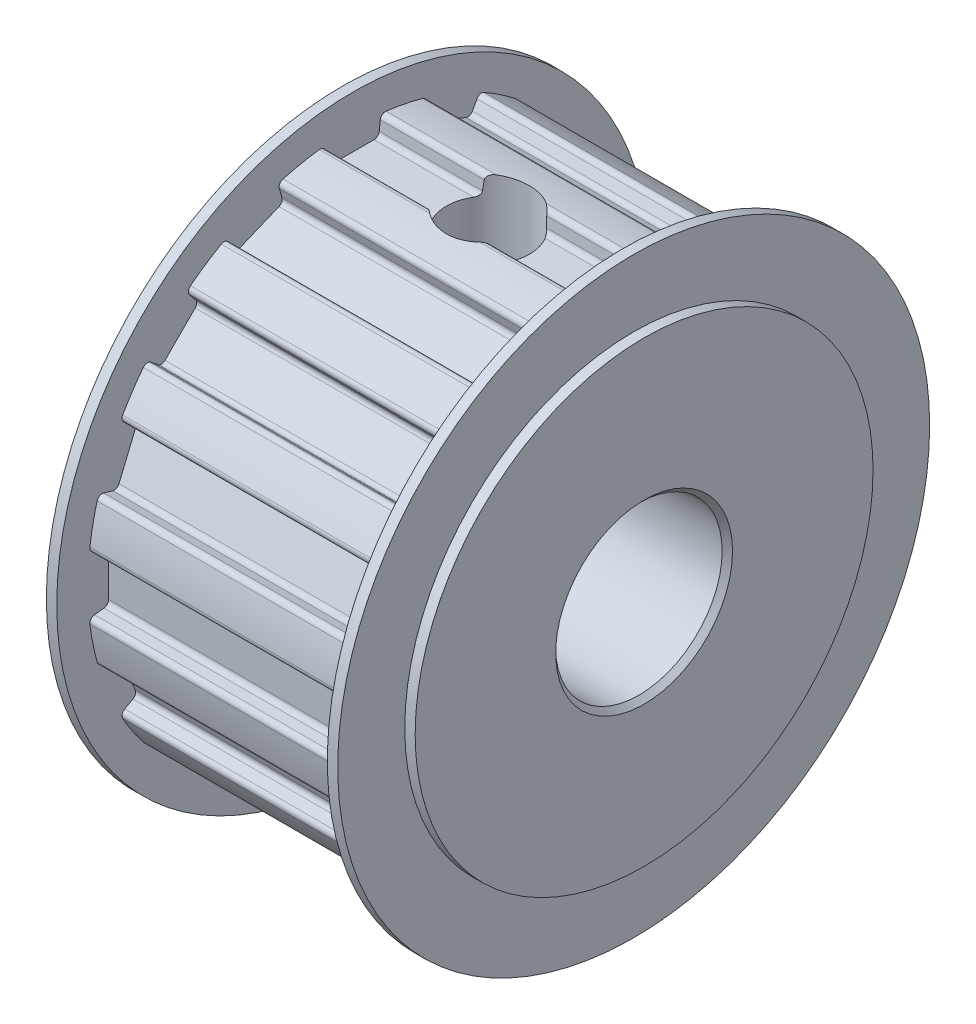
SolidWorks part; units mm, degrees
ref_plane "Plan de face" through (0, 0, 0) normal (0, 0, 1) x (1, 0, 0)
ref_plane "Plan de dessus" through (0, 0, 0) normal (0, 1, 0) x (1, 0, 0)
ref_plane "Plan de droite" through (0, 0, 0) normal (1, 0, 0) x (0, 0, -1)
sketch "Esquisse1" plane through (0, 0, 0) normal (1, 0, 0) x (0, 0, -1)
  circle A0 centre (0, 0) radius 12.73
  dimension "D1" = 25.46
extrude "Extrusion1" add sketch "Esquisse1" along normal blind 13
sketch "Esquisse22" plane through (0, 0, 0) normal (-1, 0, 0) x (0, 0, 1)
  line L0 (0, 0) -> (0, 12.73) construction
  line L1 (-1.25, 11.73) -> (1.25, 11.73)
  line L2 (0, 0) -> (1.25, 11.73) construction
  line L3 (0, 0) -> (-1.25, 11.73) construction
  line L4 (-1.25, 11.73) -> (-2.6986, 25.3234)
  line L5 (1.25, 11.73) -> (2.6979, 25.3172)
  line L6 (-2.6986, 25.3234) -> (2.6979, 25.3172)
  circle A0 centre (0, 0) radius 12.73 construction
  dimension "D1" = 2.5
  dimension "D2" = 1.25
  dimension "D3" = 1
  dimension "D4" = 180
  dimension "D5" = 180
extrude "Enlèv. mat.-Extru.2" cut sketch "Esquisse22" against normal up to next (13 mm away)
fillet "Congé1" radius 0.25 1 edges at (6.5, 11.73, -1.25)
fillet "Congé2" radius 0.25 1 edges at (6.5, 12.6583, -1.3489)
fillet "Congé3" radius 0.25 1 edges at (6.5, 11.73, 1.25)
fillet "Congé4" radius 0.25 1 edges at (6.5, 12.6583, 1.3489)
pattern_circular "Répétition circulaire1" count 16 over 360 about axis through (0, 0, 0) along (1, 0, 0) of "Enlèv. mat.-Extru.2", "Congé1", "Congé2", "Congé3", "Congé4"
sketch "Esquisse23" plane through (0, 0, 0) normal (-1, 0, 0) x (0, 0, 1)
  circle A0 centre (0, 0) radius 14.22
  dimension "D1" = 28.44
extrude "Extrusion2" add sketch "Esquisse23" along normal blind 1
sketch "Esquisse24" plane through (13, 0, 0) normal (1, 0, 0) x (0, 0, -1)
  circle A0 centre (0, 0) radius 14.22
  dimension "D1" = 28.44
extrude "Extrusion3" add sketch "Esquisse24" along normal blind 1
sketch "Esquisse25" plane through (-1, 0, 0) normal (-1, 0, 0) x (0, 0, 1)
  circle A0 centre (0, 0) radius 4
  dimension "D1" = 8
extrude "Enlèv. mat.-Extru.3" cut sketch "Esquisse25" against normal through all
sketch "Esquisse30" plane through (0, 11.73, 0) normal (0, 1, 0) x (-1, 0, 0)
  line L1 (-13, 0) -> (0, 0) construction
  line L3 (0, -1.0252) -> (0, 1.0252) construction
  circle A0 centre (-6.5, 0) radius 2
  dimension "D2" = 4
  dimension "D1" = 6.5
extrude "Enlèv. mat.-Extru.5" cut sketch "Esquisse30" against normal up to next and the other way through all
sketch "Esquisse31" plane through (-1, 0, 0) normal (-1, 0, 0) x (0, 0, 1)
  circle A0 centre (0, 0) radius 11
  dimension "D1" = 22
extrude "Enlèv. mat.-Extru.6" cut sketch "Esquisse31" against normal blind 0.5 flip side to cut
sketch "Esquisse32" plane through (14, 0, 0) normal (1, 0, 0) x (0, 0, -1)
  circle A0 centre (0, 0) radius 11
  dimension "D1" = 22
extrude "Enlèv. mat.-Extru.7" cut sketch "Esquisse32" against normal blind 0.5 flip side to cut
chamfer "Chanfrein1" distance 0.25 angle 45 1 edges at (14, 0, 4)
chamfer "Chanfrein2" distance 0.25 angle 45 1 edges at (-1, 0, 4)
